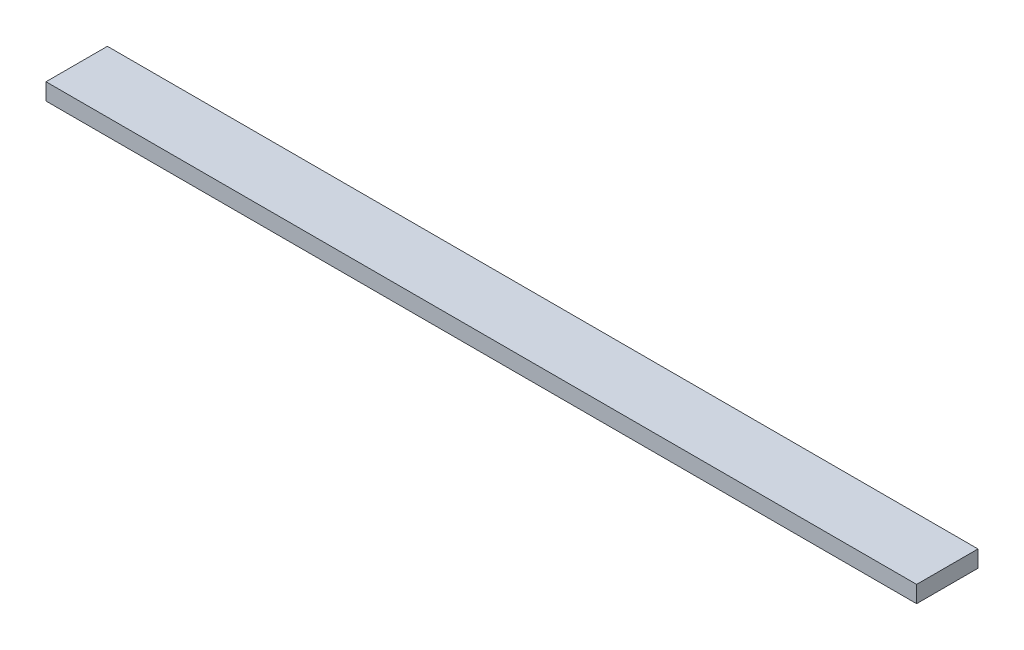
SolidWorks part; units mm, degrees
material "Pine"
ref_plane "Front Plane" through (0, 0, 0) normal (0, 0, 1) x (1, 0, 0)
ref_plane "Top Plane" through (0, 0, 0) normal (0, 1, 0) x (1, 0, 0)
ref_plane "Right Plane" through (0, 0, 0) normal (1, 0, 0) x (0, 0, -1)
sketch "Sketch1" plane through (0, 0, 0) normal (0, 1, 0) x (1, 0, 0)
  line L1 (0, 0) -> (990.6, 0)
  line L2 (0, 0) -> (0, 69.85)
  line L3 (0, 69.85) -> (990.6, 69.85)
  line L4 (990.6, 0) -> (990.6, 69.85)
  dimension "D1" = 69.85
  dimension "D2" = 990.6
extrude "Boss-Extrude1" add sketch "Sketch1" along normal blind 19.05
